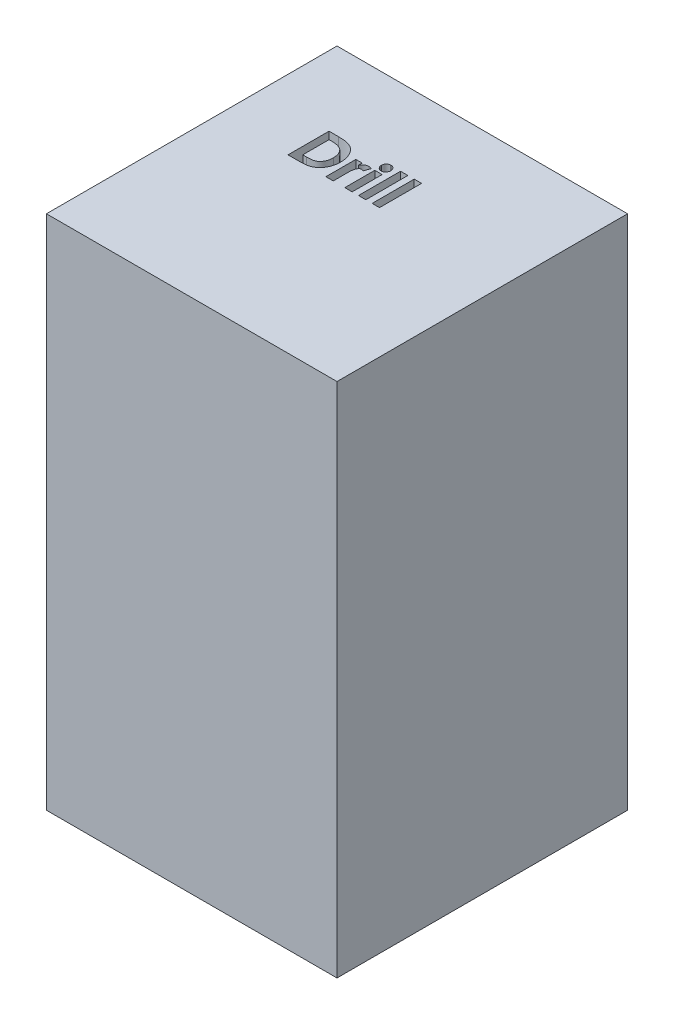
SolidWorks part; units mm, degrees
ref_plane "Front Plane" through (0, 0, 0) normal (0, 0, 1) x (1, 0, 0)
ref_plane "Top Plane" through (0, 0, 0) normal (0, 1, 0) x (1, 0, 0)
ref_plane "Right Plane" through (0, 0, 0) normal (1, 0, 0) x (0, 0, -1)
sketch "Sketch1" plane through (0, 0, 0) normal (0, 1, 0) x (1, 0, 0)
  line L1 (0, 0) -> (90, 0)
  line L2 (0, 0) -> (0, 90)
  line L3 (0, 90) -> (90, 90)
  line L4 (90, 0) -> (90, 90)
  dimension "D1" = 90
  dimension "D2" = 90
extrude "Boss-Extrude1" add sketch "Sketch1" along normal blind 160
sketch "Sketch2" plane through (0, 160, 0) normal (0, 1, 0) x (1, 0, 0)
  line L0 (20.1457, 53.2222) -> (74.8252, 53.2222) construction
  text T0 "<b>Drill</b>" font "Century Gothic" height in points 48
extrude "Cut-Extrude1" cut sketch "Sketch2" against normal blind 150
